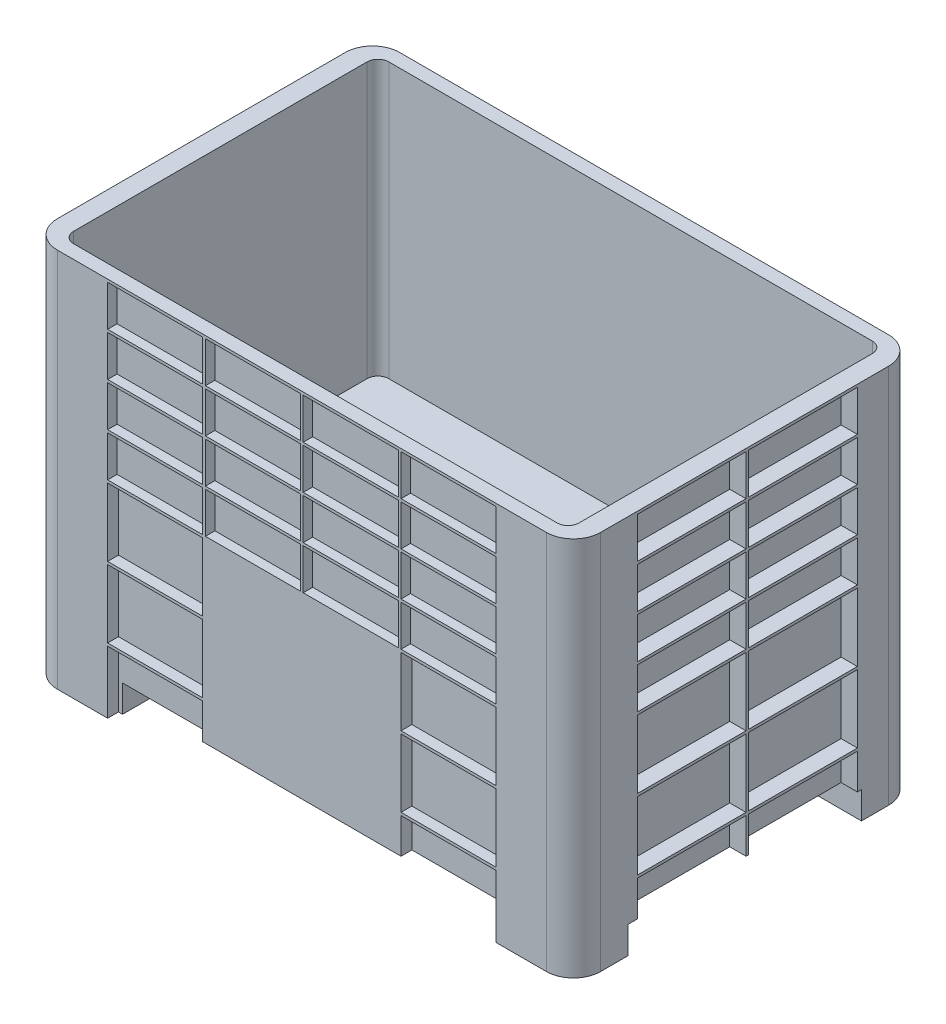
SolidWorks part; units mm, degrees
ref_plane "Vorne" through (0, 0, 0) normal (0, 0, 1) x (1, 0, 0)
ref_plane "Oben" through (0, 0, 0) normal (0, 1, 0) x (1, 0, 0)
ref_plane "Rechts" through (0, 0, 0) normal (1, 0, 0) x (0, 0, -1)
ref_plane "Ebene1" through (0, 100, 0) normal (0, 1, 0) x (1, 0, 0)
sketch "Skizze1" plane through (0, 100, 0) normal (0, 1, 0) x (1, 0, 0)
  line L1 (-450, -315) -> (450, -315)
  line L2 (-500, -265) -> (-500, 265)
  line L3 (-450, 315) -> (450, 315)
  line L4 (500, -265) -> (500, 265)
  line L5 (-500, -315) -> (500, 315) construction
  line L6 (-500, 315) -> (500, -315) construction
  arc A0 (450, -315) -> (500, -265) centre (450, -265) ccw
  arc A1 (450, 315) -> (500, 265) centre (450, 265) cw
  arc A2 (-500, 265) -> (-450, 315) centre (-450, 265) cw
  arc A3 (-450, -315) -> (-500, -265) centre (-450, -265) cw
  point P0 (0, 0)
  dimension "D3" = 50
  dimension "D1" = 630
  dimension "D2" = 1000
extrude "Aufsatz-Linear austragen1" add sketch "Skizze1" along normal blind 650
sketch "Skizze2" plane through (0, 100, 0) normal (0, -1, 0) x (1, 0, 0)
  line L0 (-450, 315) -> (450, 315) construction
  line L1 (-500, -265) -> (-500, 265) construction
  line L2 (500, 265) -> (500, -265) construction
  line L3 (450, -315) -> (-450, -315) construction
  line L4 (-450, 315) -> (450, 315)
  line L5 (-500, -265) -> (-500, 265)
  line L6 (500, 265) -> (500, -265)
  line L7 (450, -315) -> (-450, -315)
  line L9 (350, 315) -> (450, 315)
  line L10 (350, 315) -> (350, 215)
  line L11 (350, 215) -> (500, 215)
  line L12 (500, 265) -> (500, 215)
  arc A0 (500, 265) -> (450, 315) centre (450, 265) ccw construction
  arc A1 (500, 265) -> (450, 315) centre (450, 265) ccw
  arc A2 (-450, 315) -> (-500, 265) centre (-450, 265) ccw construction
  arc A3 (450, -315) -> (500, -265) centre (450, -265) ccw construction
  arc A4 (-500, -265) -> (-450, -315) centre (-450, -265) ccw construction
  arc A5 (-450, 315) -> (-500, 265) centre (-450, 265) ccw
  arc A6 (450, -315) -> (500, -265) centre (450, -265) ccw
  arc A7 (-500, -265) -> (-450, -315) centre (-450, -265) ccw
  arc M3 (500, 265) -> (450, 315) centre (450, 265) ccw
  line M4 (450, 315) -> (-450, 315)
  dimension "D1" = 150
  dimension "D2" = 100
extrude "Aufsatz-Linear austragen2" add sketch "Skizze2" along normal blind 50 contours L10 L11 L6 M3 M4
mirror "Spiegeln1" about plane through (0, 0, 0) normal (0, 0, 1) of "Aufsatz-Linear austragen2"
mirror "Spiegeln2" about plane through (0, 0, 0) normal (1, 0, 0) of "Spiegeln1", "Aufsatz-Linear austragen2"
sketch "Skizze3" plane through (0, 750, 0) normal (0, 1, 0) x (1, 0, 0)
  line L5 (445, -290) -> (-445, -290)
  line L6 (465, -270) -> (465, 270)
  line L7 (445, 290) -> (-445, 290)
  line L8 (-465, -270) -> (-465, 270)
  line L9 (465, -290) -> (-465, 290) construction
  line L10 (465, 290) -> (-465, -290) construction
  arc A4 (465, 270) -> (445, 290) centre (445, 270) ccw
  arc A5 (445, -290) -> (465, -270) centre (445, -270) ccw
  arc A6 (-445, -290) -> (-465, -270) centre (-445, -270) cw
  arc A7 (-445, 290) -> (-465, 270) centre (-445, 270) ccw
  point P11 (0, 0)
  dimension "D3" = 20
  dimension "D1" = 930
  dimension "D2" = 580
extrude "Schnitt-Linear austragen1" cut sketch "Skizze3" against normal blind 505
sketch "Skizze4" plane through (0, 0, 315) normal (0, 0, 1) x (1, 0, 0)
  line L0 (-500, 750) -> (-500, 50) construction
  line L1 (-357.5, 745) -> (-182.5, 745)
  line L2 (-357.5, 745) -> (-357.5, 670)
  line L3 (-357.5, 670) -> (-182.5, 670)
  line L4 (-182.5, 745) -> (-182.5, 670)
  line L5 (-450, 750) -> (450, 750) construction
  dimension "D1" = 175
  dimension "D2" = 75
  dimension "D3" = 142.5
  dimension "D4" = 5
extrude "Schnitt-Linear austragen2" cut sketch "Skizze4" against normal blind 17.4222
pattern_linear "Lineares Muster1" count 4 spacing 180 along (1, 0, 0) count 4 spacing 80 along (0, -1, 0) of "Schnitt-Linear austragen2"
sketch "Skizze5" plane through (0, 0, 315) normal (0, 0, 1) x (1, 0, 0)
  line L0 (-357.5, 430) -> (-182.5, 430) construction
  line L1 (-357.5, 425) -> (-182.5, 425)
  line L2 (-357.5, 425) -> (-357.5, 300)
  line L3 (-357.5, 300) -> (-182.5, 300)
  line L4 (-182.5, 425) -> (-182.5, 300)
  line L5 (-357.5, 505) -> (-357.5, 430) construction
  dimension "D1" = 5
  dimension "D2" = 175
  dimension "D3" = 125
extrude "Schnitt-Linear austragen3" cut sketch "Skizze5" against normal blind 20
pattern_linear "Lineares Muster2" count 2 spacing 540 along (1, 0, 0) count 3 spacing 130 along (0, -1, 0) of "Schnitt-Linear austragen3"
mirror "Spiegeln3" about plane through (0, 0, 0) normal (0, 0, 1) of "Lineares Muster1", "Lineares Muster2", "Schnitt-Linear austragen2", "Schnitt-Linear austragen3"
sketch "Skizze6" plane through (-500, 0, 0) normal (-1, 0, 0) x (0, 0, 1)
  line L0 (-265, 750) -> (265, 750) construction
  line L1 (-207.5, 745) -> (-7.5, 745)
  line L2 (-207.5, 745) -> (-207.5, 670)
  line L3 (-207.5, 670) -> (-7.5, 670)
  line L4 (-7.5, 745) -> (-7.5, 670)
  line L5 (-315, 750) -> (-315, 50) construction
  dimension "D1" = 5
  dimension "D2" = 75
  dimension "D3" = 200
  dimension "D4" = 107.5
extrude "Schnitt-Linear austragen4" cut sketch "Skizze6" against normal blind 30
pattern_linear "Lineares Muster3" count 2 spacing 205 along (0, 0, 1) count 4 spacing 80 along (0, -1, 0) of "Schnitt-Linear austragen4"
sketch "Skizze7" plane through (-500, 0, 0) normal (-1, 0, 0) x (0, 0, 1)
  line L0 (-207.5, 430) -> (-7.5, 430) construction
  line L1 (-207.5, 425) -> (-7.5, 425)
  line L2 (-207.5, 425) -> (-207.5, 300)
  line L3 (-207.5, 300) -> (-7.5, 300)
  line L4 (-7.5, 425) -> (-7.5, 300)
  line L5 (-207.5, 505) -> (-207.5, 430) construction
  dimension "D1" = 5
  dimension "D2" = 125
  dimension "D3" = 200
extrude "Schnitt-Linear austragen5" cut sketch "Skizze7" against normal blind 30
pattern_linear "Lineares Muster4" count 2 spacing 205 along (0, 0, 1) count 3 spacing 130 along (0, -1, 0) of "Schnitt-Linear austragen5"
mirror "Spiegeln4" about plane through (0, 0, 0) normal (1, 0, 0) of "Lineares Muster3", "Lineares Muster4", "Schnitt-Linear austragen4", "Schnitt-Linear austragen5"
